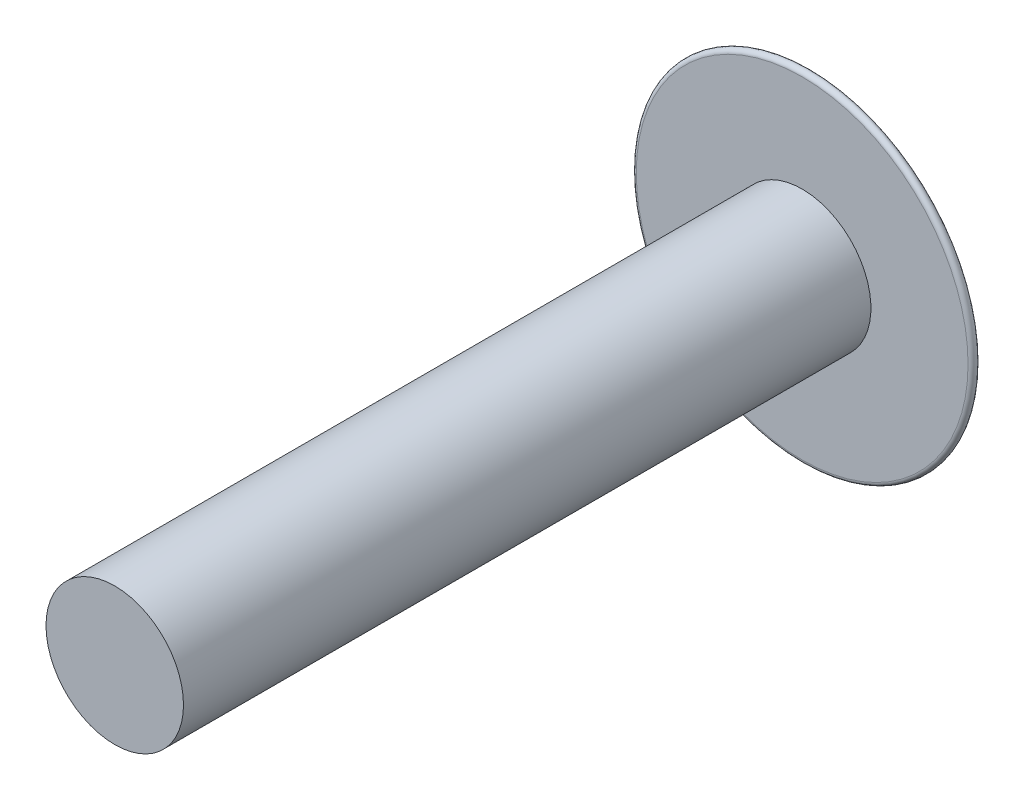
SolidWorks part; units mm, degrees
material "AISI 304"
ref_plane "Front Plane" through (0, 0, 0) normal (0, 0, 1) x (1, 0, 0)
ref_plane "Top Plane" through (0, 0, 0) normal (0, 1, 0) x (1, 0, 0)
ref_plane "Right Plane" through (0, 0, 0) normal (1, 0, 0) x (0, 0, -1)
sketch "Sketch1" plane through (0, 0, 0) normal (0, 0, 1) x (1, 0, 0)
  circle A1 centre (0, 0) radius 0.5
  dimension "D2" = 1
extrude "Boss-Extrude1" add sketch "Sketch1" along normal blind 5
cosmetic thread "Cosmetic Thread3" parameters "D2"=0.9
sketch "Sketch2" plane through (0, 0, 0) normal (1, 0, 0) x (0, 0, -1)
  line L0 (0, 0) -> (0.4, 0)
  line L1 (0, 0) -> (0, 1.3)
  arc A0 (0.4, 0) -> (0, 1.3) centre (-1.5977, 0.0969) ccw
  dimension "D2" = 2
  dimension "D1" = 1.3
  dimension "D3" = 0.4
revolve "Revolve1" add sketch "Sketch2" angle 360 about L0
fillet "Fillet1" radius 0.03 1 edges at (1.3, 0, 0)
sketch "Sketch3" plane through (0, 0, 0) normal (1, 0, 0) x (0, 0, -1)
  line L1 (0.2023, 0.15) -> (0.4023, 0.15)
  line L2 (0.2023, 0.15) -> (0.2023, -0.15)
  line L3 (0.2023, -0.15) -> (0.4023, -0.15)
  line L4 (0.4023, 0.15) -> (0.4023, -0.15)
  arc A0 (0.4023, 0.0969) -> (0.0548, 1.2236) centre (-1.5977, 0.0969) ccw construction
  point P4 (0.2023, 0)
  dimension "D1" = 0.3
  dimension "D2" = 0.2
extrude "Cut-Extrude1" cut sketch "Sketch3" against normal through all both and the other way through all
sketch "Sketch4" plane through (0, 0, 0) normal (0, 1, 0) x (1, 0, 0)
  line L1 (-0.15, 0.4016) -> (0.15, 0.4016)
  line L2 (-0.15, 0.4016) -> (-0.15, 0.2023)
  line L3 (-0.15, 0.2023) -> (0.15, 0.2023)
  line L4 (0.15, 0.4016) -> (0.15, 0.2023)
  spline S0 degree 3 poles (0.957, 0.2023) (0.8087, 0.2733) (0.6537, 0.3253) (0.3302, 0.3913) (0.1645, 0.4017) (-0.1664, 0.4016) (-0.33, 0.3912) (-0.6495, 0.3263) (-0.8083, 0.2735) (-0.957, 0.2023) knots 0 0 0 0 0.25 0.25 0.5 0.5 0.75 0.75 1 1 1 1 construction
  point P4 (0, 0.2023)
  dimension "D1" = 0.3
extrude "Cut-Extrude2" cut sketch "Sketch4" against normal mid plane 1
